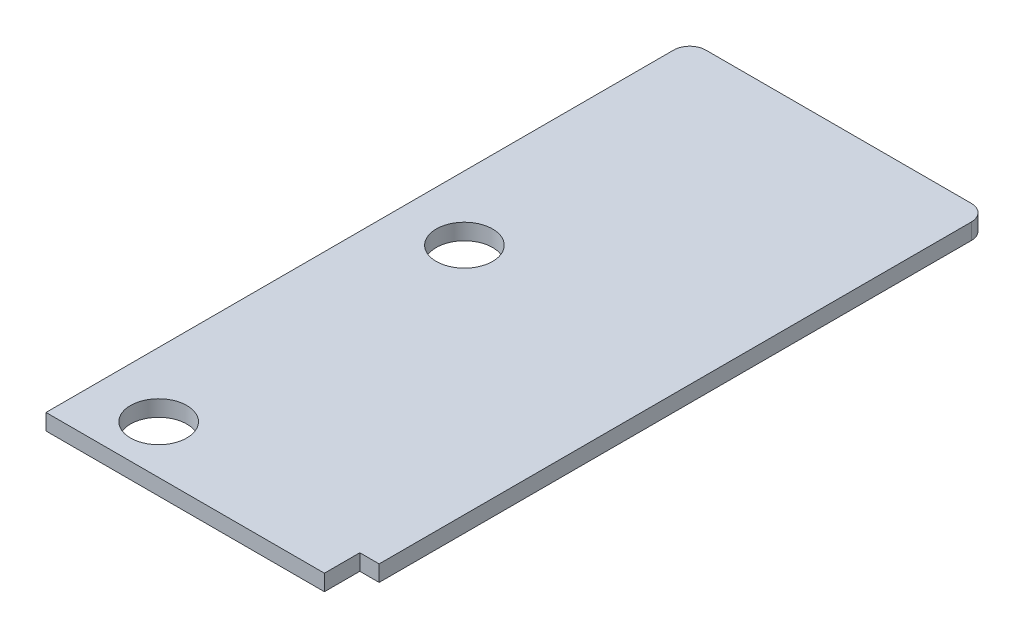
SolidWorks part; units mm, degrees
ref_plane "Alzado" through (0, 0, 0) normal (0, 0, 1) x (1, 0, 0)
ref_plane "Planta" through (0, 0, 0) normal (0, 1, 0) x (1, 0, 0)
ref_plane "Vista lateral" through (0, 0, 0) normal (1, 0, 0) x (0, 0, -1)
sketch "Croquis1" plane through (0, 0, 0) normal (0, 1, 0) x (1, 0, 0)
  line L1 (0, 0) -> (18.5, 0)
  line L2 (0, 0) -> (0, 40)
  line L3 (0, 40) -> (18.5, 40)
  line L4 (18.5, 0) -> (18.5, 40)
  circle A0 centre (4, 3) radius 1.75
  circle A1 centre (4, 22) radius 1.75
  point P9 (0, 0)
  point P10 (2.5, 22)
  point P11 (0, 0)
  point P12 (4.6633, 21.8764)
  point P13 (2.5, 22)
  dimension "D3" = 3.5
  dimension "D6" = 19
  dimension "D1" = 18.5
  dimension "D2" = 40
  dimension "D4" = 4
  dimension "D5" = 3
  dimension "D7" = 4
extrude "Saliente-Extruir1" add sketch "Croquis1" along normal blind 1
sketch "Croquis2" plane through (0, 1, 0) normal (0, 1, 0) x (1, 0, 0)
  line L1 (18.5, 0) -> (17.3, 0)
  line L2 (18.5, 0) -> (18.5, 2.2)
  line L3 (18.5, 2.2) -> (17.3, 2.2)
  line L4 (17.3, 0) -> (17.3, 2.2)
  dimension "D1" = 1.2
  dimension "D2" = 2.2
extrude "Cortar-Extruir1" cut sketch "Croquis2" against normal up to surface (1 mm away) up to face at (4, 0, -1.25)
fillet "Redondeo1" radius 1 2 edges at (0, 0.5, -40) (18.5, 0.5, -40)
